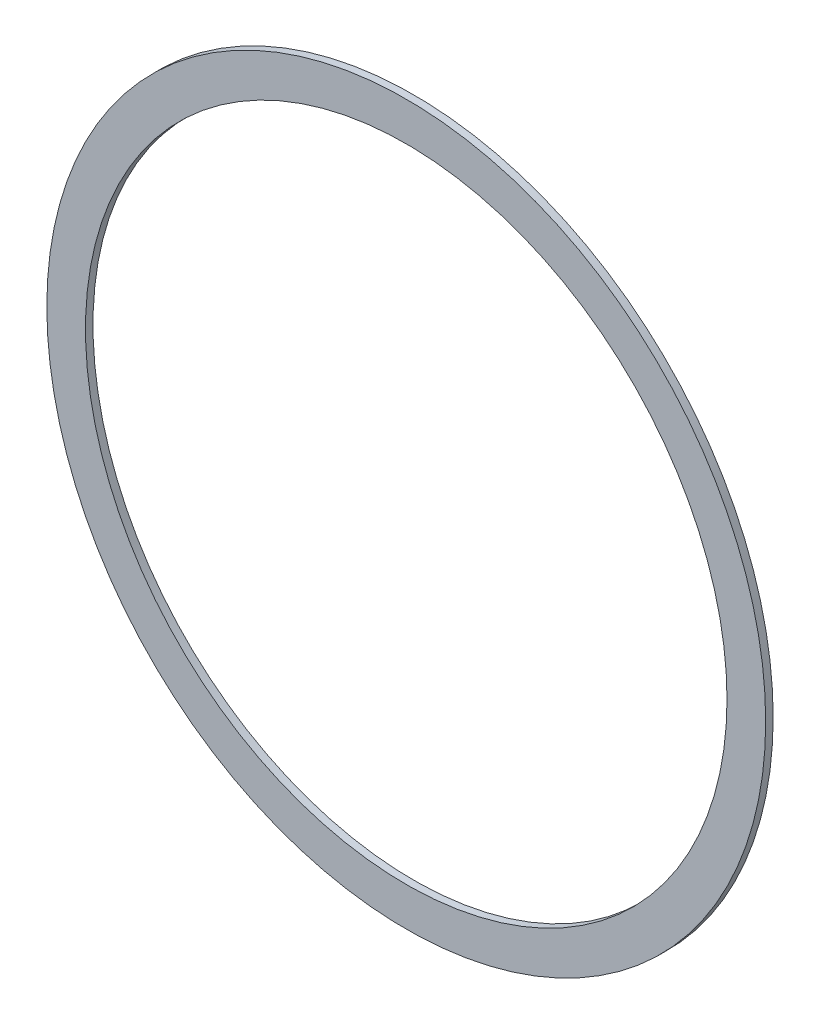
SolidWorks part; units mm, degrees
material "Rubber"
ref_plane "Front Plane" through (0, 0, 0) normal (0, 0, 1) x (1, 0, 0)
ref_plane "Top Plane" through (0, 0, 0) normal (0, 1, 0) x (1, 0, 0)
ref_plane "Right Plane" through (0, 0, 0) normal (1, 0, 0) x (0, 0, -1)
sketch "Sketch1" plane through (0, 0, 0) normal (0, 0, 1) x (1, 0, 0)
  line L0 (0, 19.05) -> (-1.4329, 19.05) construction
  line L1 (0, 17) -> (1.549, 17) construction
  line L4 (0, 0) -> (-25.8311, 0) construction
  circle A2 centre (0, 0) radius 19.05
  circle A3 centre (0, 0) radius 17
  dimension "D2" = 19.05
  dimension "D3" = 17
extrude "Boss-Extrude1" add sketch "Sketch1" along normal blind 0.3969
